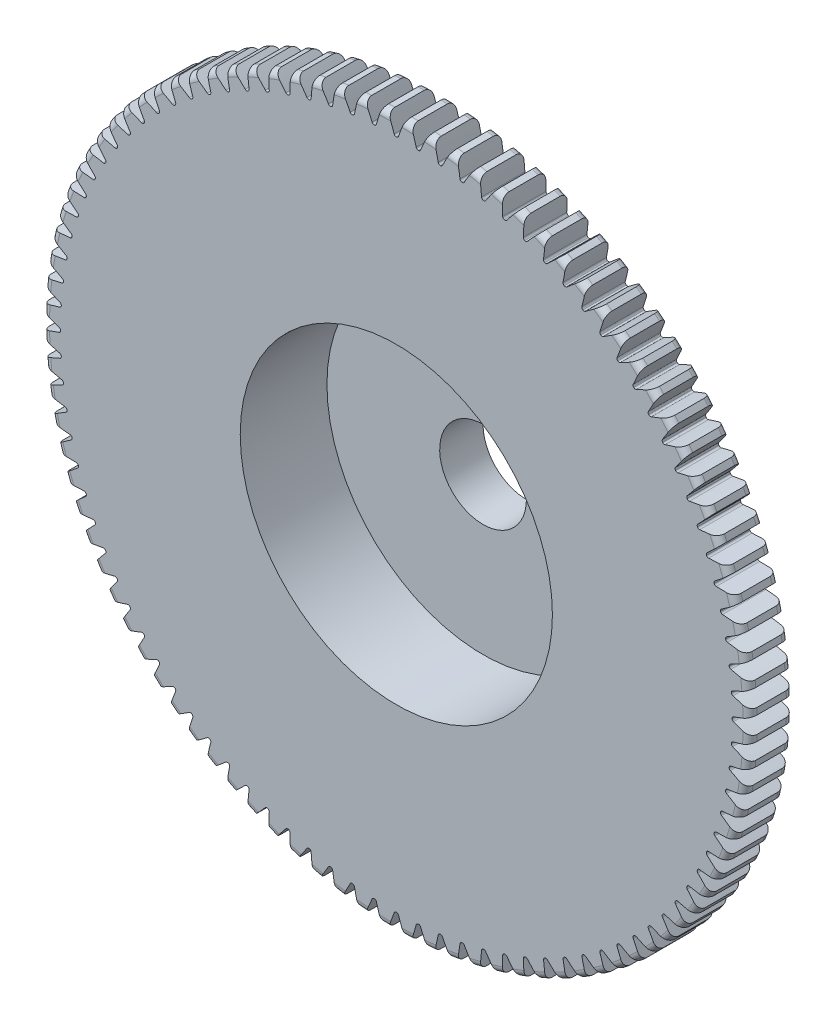
SolidWorks part; units mm, degrees
ref_plane "Front Plane" through (0, 0, 0) normal (0, 0, 1) x (1, 0, 0)
ref_plane "Top Plane" through (0, 0, 0) normal (0, 1, 0) x (1, 0, 0)
ref_plane "Right Plane" through (0, 0, 0) normal (1, 0, 0) x (0, 0, -1)
sketch "Sketch1" plane through (0, 0, 0) normal (0, 0, 1) x (1, 0, 0)
  line L0 (-1219.2, 0) -> (1219.2, 0) construction
  circle A0 centre (0, 0) radius 25.908 construction
  circle A1 centre (0, 0) radius 25.4 construction
  circle A2 centre (0, 0) radius 24.5851 construction
  circle A3 centre (0, 0) radius 7.7343 construction
  circle A4 centre (0, 0) radius 3.175 construction
  dimension "D2" = 0.508
  dimension "D3" = 1.3229
  dimension "D1" = 1.3229
sketch "Sketch2" plane through (0, 0, 0) normal (1, 0, 0) x (0, 0, -1)
  line L0 (0, 0) -> (-3.175, 0) construction
  line L1 (-3.175, 0) -> (-9.525, 0) construction
  dimension "Overall Width" = 9.525
  dimension "Face Width" = 3.175
sketch "Sketch4" plane through (0, 0, 0) normal (1, 0, 0) x (0, 0, -1)
  line L0 (-9.525, 3.175) -> (-9.525, 7.7343)
  line L1 (-9.525, 7.7343) -> (-3.175, 7.7343)
  line L2 (-3.175, 7.7343) -> (-3.175, 25.908)
  line L3 (-3.175, 25.908) -> (0, 25.908)
  line L4 (0, 25.908) -> (0, 3.175)
  line L5 (-3.175, 7.7343) -> (-3.175, 0) construction
  line L6 (0, 25.908) -> (0, -25.908) construction
  line L7 (-3.175, 7.7343) -> (0, 7.7343) construction
  line L12 (-9.525, 3.175) -> (0, 3.175)
revolve "Revolve1" add sketch "Sketch4" angle 360 about L1
fillet "Fillet2" radius 0.5182 4 edges at (0, 7.7343, 9.525) (0, 7.7343, 3.175) (0, 25.908, 3.175) (0, 25.908, 0)
sketch "Sketch7" plane through (0, 0, 3.175) normal (0, 0, 1) x (1, 0, 0)
  line L0 (0, 0) -> (0, 25.908) construction
  line L1 (0.4156, 25.3966) -> (0.6085, 25.9009) construction
  line L3 (0.8477, 25.8941) -> (0.8311, 25.3864) construction
  line L4 (0.8311, 25.3864) -> (0.8044, 24.5719) construction
  line L5 (0, 0) -> (0.8044, 24.5719) construction
  line L6 (0.4156, 25.3966) -> (0, 0) construction
  line L7 (0.4156, 25.3966) -> (0.4239, 25.9045) construction
  line L8 (0.4156, 25.3966) -> (0, 0) construction
  circle A0 centre (0, 0) radius 25.908 construction
  arc A1 (-0.0078, 24.5851) -> (0.0078, 24.5851) centre (0, 0) cw
  circle A2 centre (0, 0) radius 24.5851 construction
  arc A3 (-0.4156, 25.3966) -> (0.4156, 25.3966) centre (0, 0) cw construction
  circle A4 centre (0, 0) radius 25.4 construction
  arc A5 (1.0806, 25.8855) -> (0.6147, 25.9007) centre (0, 0) ccw construction
  arc A6 (0.4156, 25.3966) -> (1.2463, 25.3694) centre (0, 0) cw construction
  arc A7 (-0.6147, 25.9007) -> (0.6147, 25.9007) centre (0, 0) cw
  arc A8 (0.1577, 24.6915) -> (0.6147, 25.9007) centre (24.1384, 16.3199) cw
  arc A9 (-0.1577, 24.6915) -> (-0.6147, 25.9007) centre (-24.1384, 16.3199) ccw
  arc A10 (-0.0078, 24.5851) -> (-0.1577, 24.6915) centre (-0.0078, 24.7438) cw
  arc A11 (0.0078, 24.5851) -> (0.1577, 24.6915) centre (0.0078, 24.7438) ccw
  point P26 (-0.1207, 24.5848)
  point P29 (0.1207, 24.5848)
  dimension "D4" = 0.1588
  dimension "D5" = 25.4
  dimension "D3" = 20
  dimension "D1" = 1.6624
  dimension "D2" = 0.8312
extrude "Cut-Extrude2" cut sketch "Sketch7" against normal through all
pattern_circular "CirPattern1" count 96 over 360 about axis through (0, 0, 0) along (0, 0, 1) of "Cut-Extrude2"
sketch "Sketch8" plane through (0, 0, 9.525) normal (0, 0, 1) x (1, 0, 0)
  circle A0 centre (0, 0) radius 9.5361
sketch "Sketch9" plane through (0, 0, 0) normal (0, 0, -1) x (-1, 0, 0)
  circle A0 centre (0, 0) radius 3
  circle A1 centre (0, 0) radius 3.8854
extrude "Cut-Extrude3" cut sketch "Sketch8" against normal up to surface (6.35 mm away) up to face at (0, 0, 3.175)
sketch "Sketch13" plane through (0, 0, 0) normal (0, 0, -1) x (-1, 0, 0)
  circle A0 centre (0, 0) radius 12.7
  dimension "D1" = 25.4
extrude "Boss-Extrude1" add sketch "Sketch13" along normal blind 6.35
fillet "Fillet3" radius 1.27 1 edges at (0, 12.7, -6.35)
sketch "Sketch12" plane through (0, 0, 3.175) normal (0, 0, 1) x (1, 0, 0)
  circle A0 centre (0, 0) radius 11.43
  dimension "D1" = 22.86
extrude "Cut-Extrude4" cut sketch "Sketch12" against normal blind 6.35
fillet "Fillet4" radius 1.27 1 edges at (0, 12.7, 0)
sketch "Sketch14" plane through (0, 0, -6.35) normal (0, 0, -1) x (-1, 0, 0)
  circle A0 centre (0, 0) radius 3.175
  dimension "D1" = 6.35
extrude "Cut-Extrude5" cut sketch "Sketch14" against normal through all
equation "\"D1@Sketch1\"=2.5*(\"Pitch Dia.@Sketch1\"/\"Number of Teeth@Sketch1\")"
equation "\"D1@CirPattern1\"=\"Number of Teeth@Sketch1\""
equation "\"D1@Fillet2\"=\"OD@Sketch1\"*.01"
equation "\"D1@Sketch7\"=3.14159*(\"Pitch Dia.@Sketch1\"/\"Number of Teeth@Sketch1\")"
equation "\"D2@Sketch7\"=\"D1@Sketch7\"/2"
equation "\"D4@Sketch7\"=\"D1@Sketch7\"*.0955"
equation "\"D5@Sketch7\"=\"Pitch Dia.@Sketch1\"/2"
